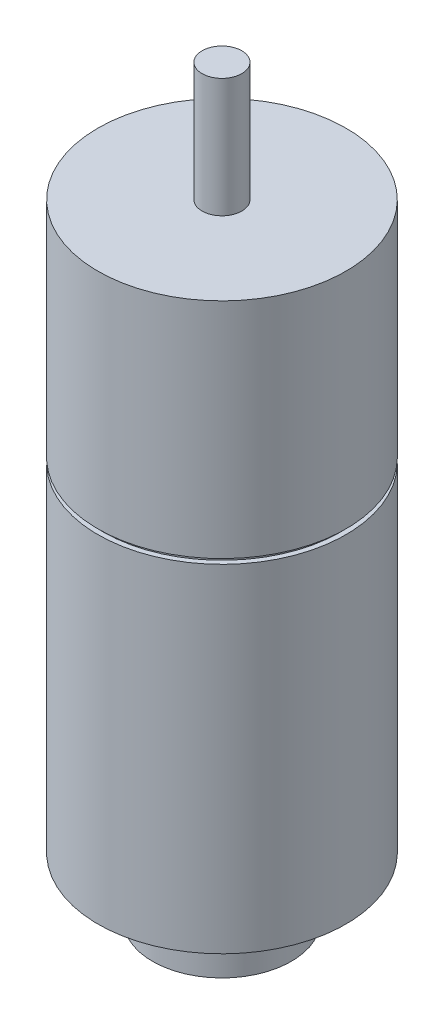
SolidWorks part; units mm, degrees
material "Aço inoxidável fundido"
ref_plane "Plano frontal" through (0, 0, 0) normal (0, 0, 1) x (1, 0, 0)
ref_plane "Plano superior" through (0, 0, 0) normal (0, 1, 0) x (1, 0, 0)
ref_plane "Plano direito" through (0, 0, 0) normal (1, 0, 0) x (0, 0, -1)
sketch "Esboço1" plane through (0, 0, 0) normal (0, 0, 1) x (1, 0, 0)
  line L0 (0, 0) -> (7, 0)
  line L1 (12.5, 6) -> (12.5, 40)
  line L2 (12.5, 40) -> (12, 40)
  line L3 (12, 40) -> (12, 40.5)
  line L4 (12, 40.5) -> (12.5, 40.5)
  line L5 (12.5, 40.5) -> (12.5, 63)
  line L6 (12.5, 63) -> (2, 63)
  line L7 (2, 63) -> (2, 75)
  line L8 (2, 75) -> (0, 75)
  line L9 (0, 75) -> (0, 0) construction
  line L10 (7, 0) -> (7, 5)
  line L11 (6, 6) -> (12.5, 6)
  line L12 (7, 5) -> (6, 5)
  line L13 (6, 5) -> (6, 6)
  line L14 (0, 0) -> (0, 75)
  dimension "D1" = 0.5
  dimension "D2" = 4
  dimension "D3" = 40
  dimension "D4" = 25
  dimension "D5" = 34
  dimension "D6" = 14
  dimension "D7" = 23
  dimension "D8" = 12
  dimension "D9" = 1
revolve "Revolução1" add sketch "Esboço1" angle 360 about L9
